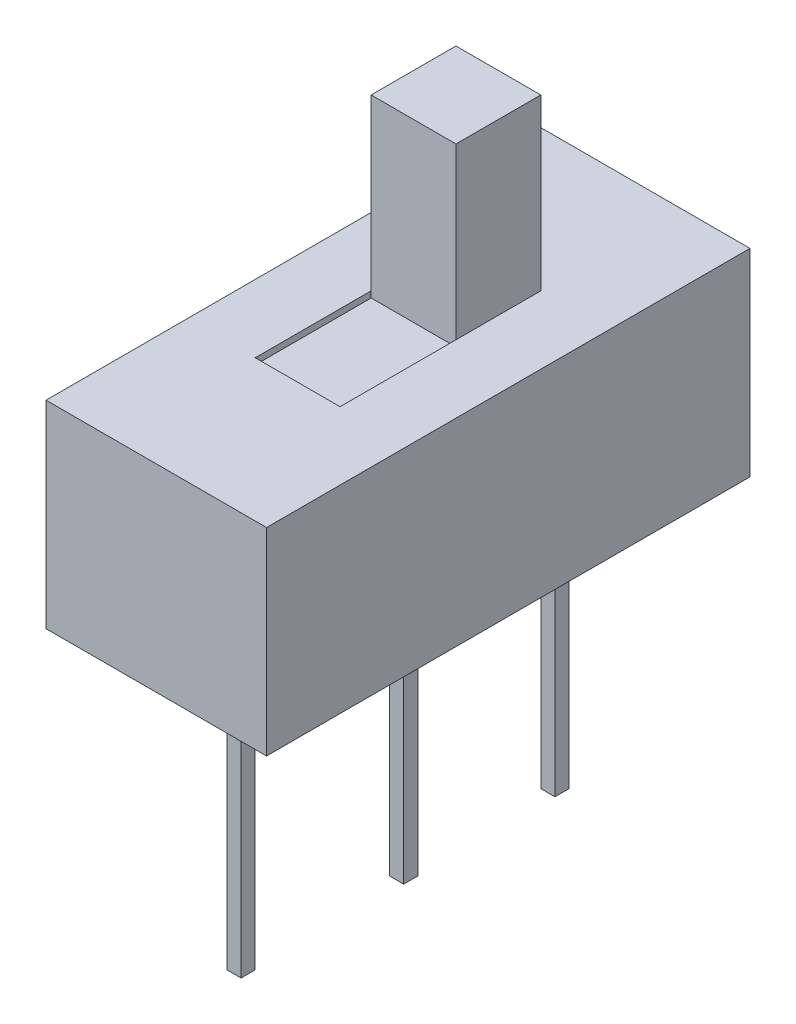
SolidWorks part; units mm, degrees
ref_plane "Front Plane" through (0, 0, 0) normal (0, 0, 1) x (1, 0, 0)
ref_plane "Top Plane" through (0, 0, 0) normal (0, 1, 0) x (1, 0, 0)
ref_plane "Right Plane" through (0, 0, 0) normal (1, 0, 0) x (0, 0, -1)
ref_plane "Plane1" through (0, 3.5, 0) normal (0, 1, 0) x (1, 0, 0)
sketch "Sketch1" plane through (0, 3.5, 0) normal (0, 1, 0) x (1, 0, 0)
  line L0 (3.9, 8.55) -> (0, 8.55)
  line L1 (0, 8.55) -> (0, 0)
  line L2 (0, 0) -> (3.9, 0)
  line L3 (3.9, 0) -> (3.9, 8.55)
extrude "Boss-Extrude1" add sketch "Sketch1" against normal blind 3.5
ref_plane "Plane2" through (2.7, 0, 0) normal (1, 0, 0) x (0, 0, -1)
sketch "Sketch2" plane through (2.7, 0, 0) normal (1, 0, 0) x (0, 0, -1)
  line L0 (6.05, 6.5) -> (4.55, 6.5)
  line L1 (4.55, 6.5) -> (4.55, 3.5)
  line L2 (4.55, 3.5) -> (6.05, 3.5)
  line L3 (6.05, 3.5) -> (6.05, 6.5)
extrude "Boss-Extrude2" add sketch "Sketch2" against normal blind 1.5
sketch "Sketch3" plane through (2.7, 0, 0) normal (1, 0, 0) x (0, 0, -1)
  line L0 (4.55, 3.5) -> (2.5, 3.5)
  line L1 (2.5, 3.5) -> (2.5, 3.39)
  line L2 (2.5, 3.39) -> (4.55, 3.39)
  line L3 (4.55, 3.39) -> (4.55, 3.5)
extrude "Cut-Extrude1" cut sketch "Sketch3" against normal blind 1.5
sketch "Sketch4" plane through (0, 0, 0) normal (0, -1, 0) x (1, 0, 0)
  line L0 (2.075, -6.925) -> (2.075, -7.175)
  line L1 (2.075, -7.175) -> (1.825, -7.175)
  line L2 (1.825, -7.175) -> (1.825, -6.925)
  line L3 (1.825, -6.925) -> (2.075, -6.925)
extrude "Boss-Extrude3" add sketch "Sketch4" along normal blind 5
sketch "Sketch5" plane through (0, 0, 0) normal (0, -1, 0) x (1, 0, 0)
  line L0 (2.075, -1.375) -> (2.075, -1.625)
  line L1 (2.075, -1.625) -> (1.825, -1.625)
  line L2 (1.825, -1.625) -> (1.825, -1.375)
  line L3 (1.825, -1.375) -> (2.075, -1.375)
extrude "Boss-Extrude4" add sketch "Sketch5" along normal blind 5
sketch "Sketch6" plane through (0, 0, 0) normal (0, -1, 0) x (1, 0, 0)
  line L0 (2.075, -4.25) -> (2.075, -4.5)
  line L1 (2.075, -4.5) -> (1.825, -4.5)
  line L2 (1.825, -4.5) -> (1.825, -4.25)
  line L3 (1.825, -4.25) -> (2.075, -4.25)
extrude "Boss-Extrude5" add sketch "Sketch6" along normal blind 5
